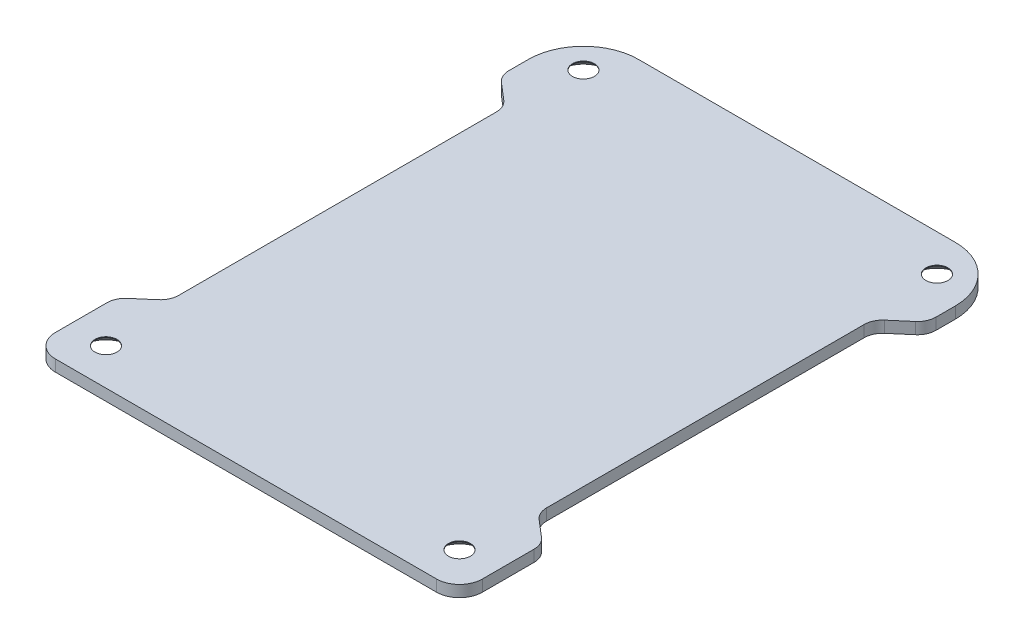
SolidWorks part; units mm, degrees
material "Perspex (TM) GS Acrylic Cast Sheet"
ref_plane "Front Plane" through (0, 0, 0) normal (0, 0, 1) x (1, 0, 0)
ref_plane "Top Plane" through (0, 0, 0) normal (0, 1, 0) x (1, 0, 0)
ref_plane "Right Plane" through (0, 0, 0) normal (1, 0, 0) x (0, 0, -1)
sketch "Sketch1" plane through (0, 0, 0) normal (0, 1, 0) x (1, 0, 0)
  line L0 (0, -1000) -> (0, 49000) construction
  line L1 (-26.3525, -38.1) -> (26.3525, -38.1)
  line L2 (-29.5275, -34.925) -> (-29.5275, -27.7953)
  line L3 (-21.9075, 38.1) -> (21.9075, 38.1)
  line L4 (-28.6384, -25.8649) -> (-26.3342, -23.8943)
  line L5 (-29.5275, -38.1) -> (29.5275, 38.1) construction
  line L6 (-29.5275, 38.1) -> (29.5275, -38.1) construction
  line L7 (-1000, 0) -> (49000, 0) construction
  line L8 (-25.4451, -21.964) -> (-25.4451, 21.964)
  line L9 (25.4451, -21.964) -> (25.4451, 21.964)
  line L10 (28.6384, -25.8649) -> (26.3342, -23.8943)
  line L11 (29.5275, -34.925) -> (29.5275, -27.7953)
  line L12 (29.5275, 30.48) -> (29.5275, 27.7953)
  line L13 (28.6384, 25.8649) -> (26.3342, 23.8943)
  line L14 (-28.6384, 25.8649) -> (-26.3342, 23.8943)
  line L15 (-29.5275, 30.48) -> (-29.5275, 27.7953)
  circle A0 centre (24.4475, 33.02) radius 1.524
  circle A1 centre (-24.4475, -33.02) radius 1.524
  circle A2 centre (-24.4475, 33.02) radius 1.524
  circle A3 centre (24.4475, -33.02) radius 1.524
  arc A4 (-29.5275, 30.48) -> (-21.9075, 38.1) centre (-21.9075, 30.48) cw
  arc A5 (21.9075, 38.1) -> (29.5275, 30.48) centre (21.9075, 30.48) cw
  arc A6 (-26.3525, -38.1) -> (-29.5275, -34.925) centre (-26.3525, -34.925) cw
  arc A7 (26.3525, -38.1) -> (29.5275, -34.925) centre (26.3525, -34.925) ccw
  arc A8 (-29.5275, -27.7953) -> (-28.6384, -25.8649) centre (-26.9875, -27.7953) cw
  arc A9 (-26.3342, -23.8943) -> (-25.4451, -21.964) centre (-27.9851, -21.964) ccw
  arc A10 (28.6384, -25.8649) -> (29.5275, -27.7953) centre (26.9875, -27.7953) cw
  arc A11 (25.4451, -21.964) -> (26.3342, -23.8943) centre (27.9851, -21.964) ccw
  arc A12 (29.5275, 27.7953) -> (28.6384, 25.8649) centre (26.9875, 27.7953) cw
  arc A13 (26.3342, 23.8943) -> (25.4451, 21.964) centre (27.9851, 21.964) ccw
  arc A14 (-26.3342, 23.8943) -> (-25.4451, 21.964) centre (-27.9851, 21.964) cw
  arc A15 (-28.6384, 25.8649) -> (-29.5275, 27.7953) centre (-26.9875, 27.7953) cw
  point P0 (0, 0)
  point P24 (25.4451, 0)
  point P25 (-25.4451, 0)
  point P46 (-29.5275, -26.6253)
  point P49 (-25.4451, -23.1339)
  point P52 (29.5275, -26.6253)
  point P55 (25.4451, -23.1339)
  point P58 (29.5275, 26.6253)
  point P61 (25.4451, 23.1339)
  point P64 (-25.4451, 23.1339)
  point P67 (-29.5275, 26.6253)
  dimension "D3" = 3.048
  dimension "D6" = 7.62
  dimension "D7" = 3.175
  dimension "D8" = 2.54
  dimension "D1" = 59.055
  dimension "D2" = 76.2
  dimension "D4" = 5.08
  dimension "D5" = 5.08
extrude "Boss-Extrude1" add sketch "Sketch1" along normal blind 1.5875
chamfer "Chamfer1" distance 1.7145 angle 41 4 edges at (-24.4475, 0, -34.544) (-24.4475, 0, 34.544) (24.4475, 0, 31.496) (24.4475, 0, -31.496)
